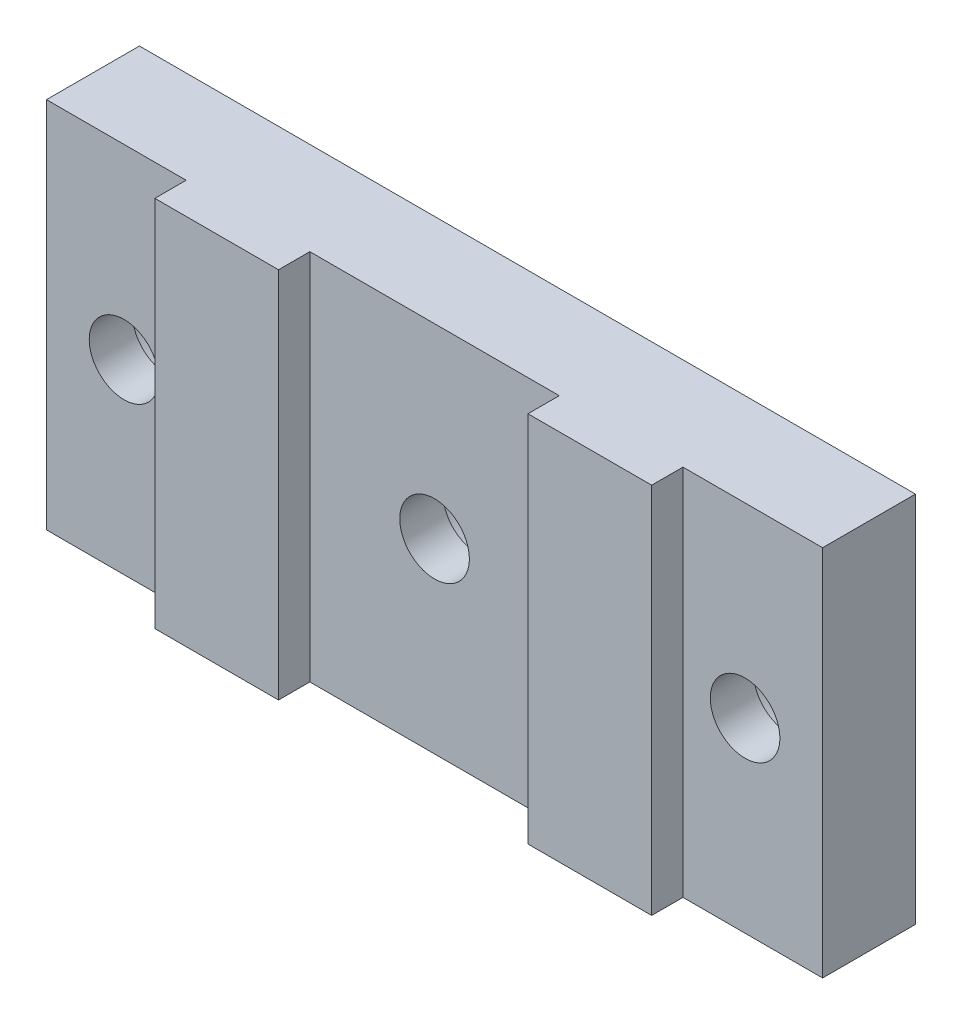
SolidWorks part; units mm, degrees
ref_plane "Front Plane" through (0, 0, 0) normal (0, 0, 1) x (1, 0, 0)
ref_plane "Top Plane" through (0, 0, 0) normal (0, 1, 0) x (1, 0, 0)
ref_plane "Right Plane" through (0, 0, 0) normal (1, 0, 0) x (0, 0, -1)
sketch "Sketch1" plane through (0, 0, 0) normal (0, 0, 1) x (1, 0, 0)
  line L1 (0, 0) -> (39.6748, 0)
  line L2 (0, 0) -> (0, 19.05)
  line L3 (0, 19.05) -> (39.6748, 19.05)
  line L4 (39.6748, 0) -> (39.6748, 19.05)
  dimension "D1" = 19.05
  dimension "D2" = 39.6748
extrude "Extrude1" add sketch "Sketch1" along normal blind 6.35
sketch "Sketch2" plane through (0, 0, 0) normal (0, -1, 0) x (1, 0, 0)
  line L0 (0, 6.35) -> (39.6748, 6.35) construction
  line L1 (0, 6.35) -> (7.1374, 6.35)
  line L2 (0, 6.35) -> (0, 4.7498)
  line L3 (0, 4.7498) -> (7.1374, 4.7498)
  line L4 (7.1374, 6.35) -> (7.1374, 4.7498)
  line L5 (13.462, 6.35) -> (26.2128, 6.35)
  line L6 (13.462, 6.35) -> (13.462, 4.7498)
  line L7 (13.462, 4.7498) -> (26.2128, 4.7498)
  line L8 (26.2128, 6.35) -> (26.2128, 4.7498)
  line L9 (0, 6.35) -> (0, 0) construction
  line L10 (39.6748, 6.35) -> (32.5374, 6.35)
  line L11 (39.6748, 6.35) -> (39.6748, 4.7498)
  line L12 (39.6748, 4.7498) -> (32.5374, 4.7498)
  line L13 (32.5374, 6.35) -> (32.5374, 4.7498)
  dimension "D1" = 1.6002
  dimension "D2" = 7.1374
  dimension "D3" = 13.462
  dimension "D4" = 26.2128
  dimension "D5" = 32.5374
extrude "Cut-Extrude1" cut sketch "Sketch2" against normal through all
hole_wizard "Hole1" positions "Sketch4" profile "Sketch5" legacy end condition through all
sketch "Sketch4" plane through (0, 0, 0) normal (0, 0, -1) x (-1, 0, 0)
  line L0 (0, 0) -> (-39.6748, 0) construction
  line L1 (0, 19.05) -> (0, 0) construction
  point P0 (-3.9624, 9.525)
  point P1 (-19.8374, 9.525)
  point P3 (-35.7124, 9.525)
  dimension "D1" = 9.525
  dimension "D2" = 3.9624
  dimension "D3" = 15.875
  dimension "D4" = 31.75
sketch "Sketch5" plane through (3.9624, 9.525, 0) normal (1, 0, 0) x (0, 1, 0)
  line L0 (0, 0) -> (0, 6.35)
  line L1 (0, 6.35) -> (1.778, 6.35)
  line L2 (1.778, 6.35) -> (1.778, 2.54)
  line L3 (1.778, 2.54) -> (3.175, 2.54)
  line L4 (3.175, 2.54) -> (3.175, 0)
  line L5 (3.175, 0) -> (0, 0)
  line L6 (0, 110) -> (0, -10) construction
  dimension "Diameter" = 3.556
  dimension "Depth" = 6.35
  dimension "C-Bore Diameter" = 6.35
  dimension "C-Bore Depth" = 2.54
